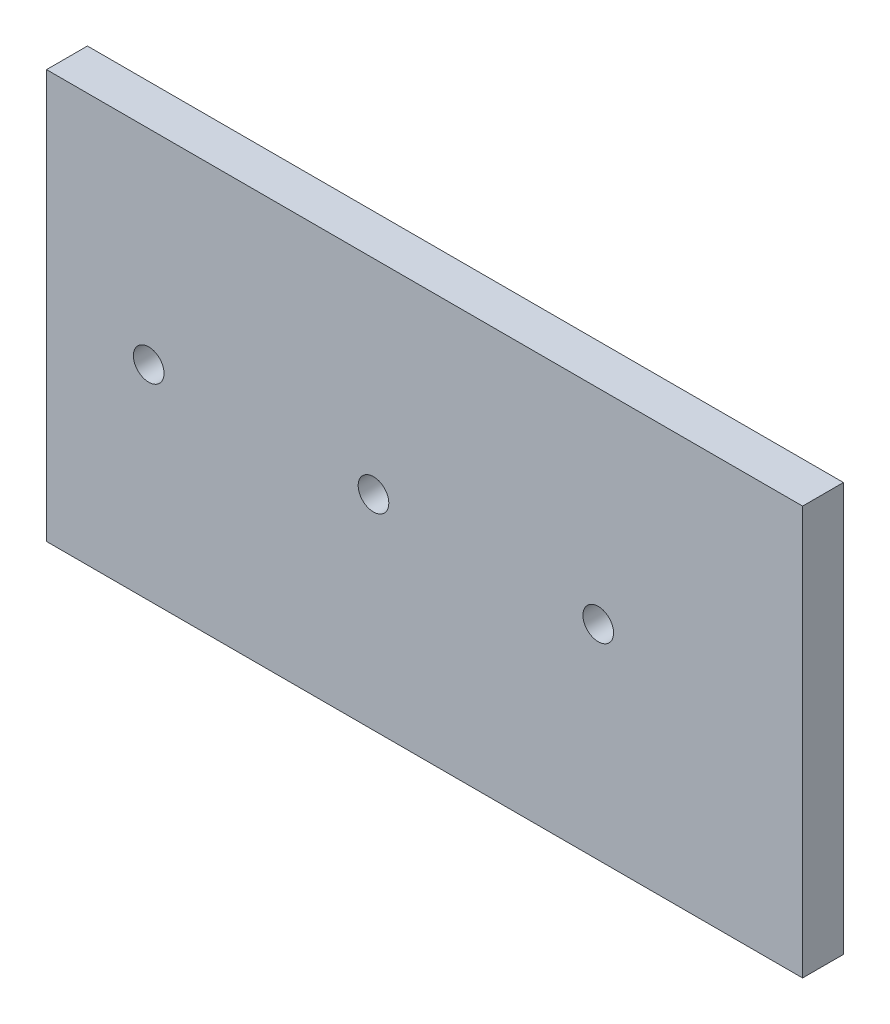
SolidWorks part; units mm, degrees
ref_plane "Front Plane" through (0, 0, 0) normal (0, 0, 1) x (1, 0, 0)
ref_plane "Top Plane" through (0, 0, 0) normal (0, 1, 0) x (1, 0, 0)
ref_plane "Right Plane" through (0, 0, 0) normal (1, 0, 0) x (0, 0, -1)
sketch "Sketch1" plane through (0, 0, 0) normal (0, 0, 1) x (1, 0, 0)
  line L1 (0, 0) -> (234.95, 0)
  line L2 (0, 0) -> (0, 127)
  line L3 (0, 127) -> (234.95, 127)
  line L4 (234.95, 0) -> (234.95, 127)
  circle A0 centre (31.75, 63.5) radius 4.7625
  circle A1 centre (101.6, 63.5) radius 4.7625
  circle A2 centre (171.45, 63.5) radius 4.7625
  dimension "D5" = 9.525
  dimension "D1" = 31.75
  dimension "D2" = 234.95
  dimension "D3" = 63.5
  dimension "D4" = 127
  dimension "D7" = 69.85
  dimension "D6" = 3
extrude "Boss-Extrude1" add sketch "Sketch1" along normal blind 12.7
